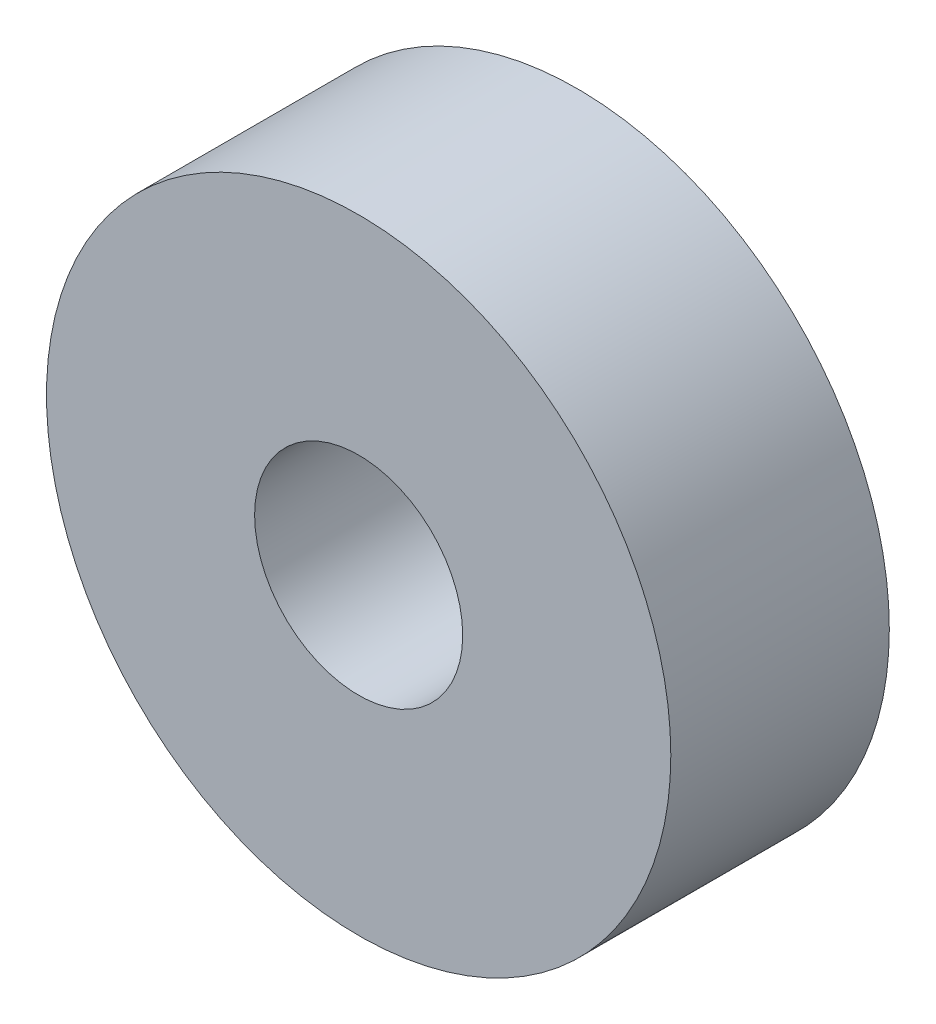
SolidWorks part; units mm, degrees
ref_plane "前视基准面" through (0, 0, 0) normal (0, 0, 1) x (1, 0, 0)
ref_plane "上视基准面" through (0, 0, 0) normal (0, 1, 0) x (1, 0, 0)
ref_plane "右视基准面" through (0, 0, 0) normal (1, 0, 0) x (0, 0, -1)
sketch "草图1" plane through (0, 0, 0) normal (0, 0, 1) x (1, 0, 0)
  circle A0 centre (0, 0) radius 5
  circle A1 centre (0, 0) radius 15
extrude "凸台-拉伸1" add sketch "草图1" along normal blind 10.5
